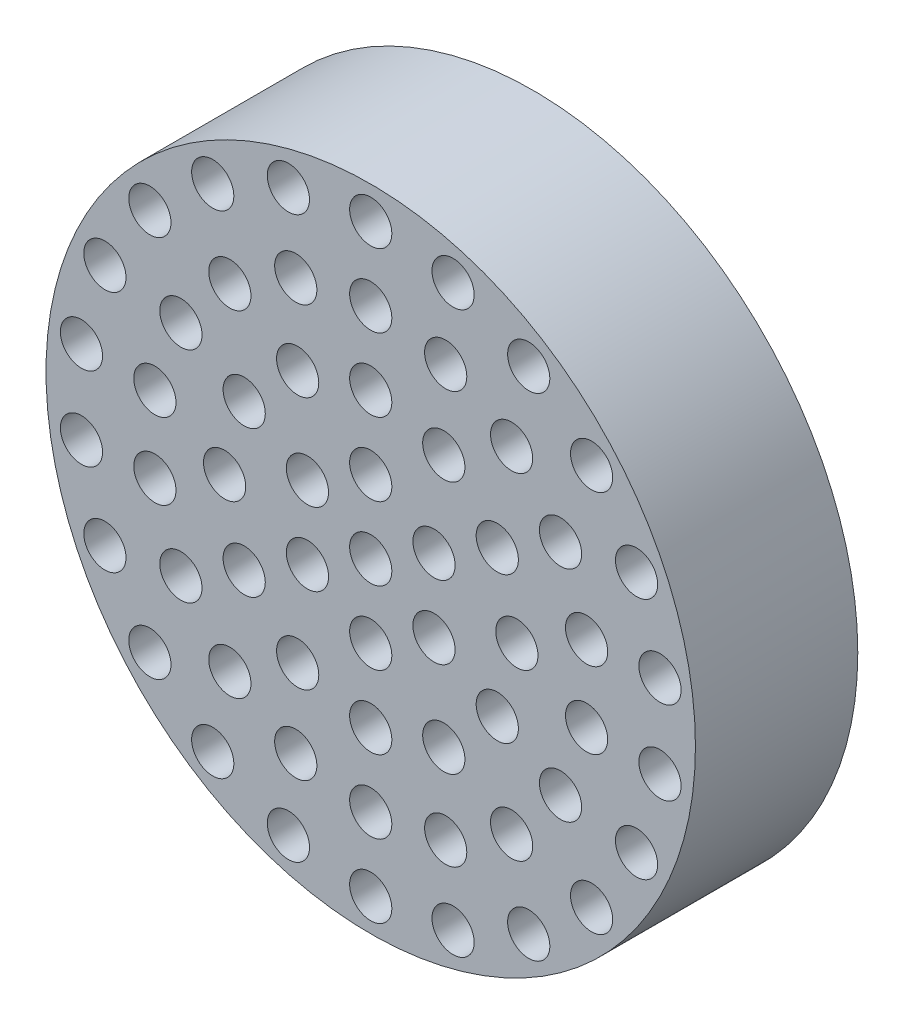
SolidWorks part; units mm, degrees
ref_plane "Plan de face" through (0, 0, 0) normal (0, 0, 1) x (1, 0, 0)
ref_plane "Plan de dessus" through (0, 0, 0) normal (0, 1, 0) x (1, 0, 0)
ref_plane "Plan de droite" through (0, 0, 0) normal (1, 0, 0) x (0, 0, -1)
sketch "Esquisse1" plane through (0, 0, 0) normal (0, 0, 1) x (1, 0, 0)
  line L0 (0, 0) -> (57.9765, 0) construction
  line L1 (0, 0) -> (0, 27.5754) construction
  circle A101 centre (0, 0) radius 20
  dimension "D1" = 40
extrude "Boss.-Extru.1" add sketch "Esquisse1" along normal blind 10
sketch "Esquisse2" plane through (0, 0, 10) normal (0, 0, 1) x (1, 0, 0)
  circle A1 centre (0, 4.5) radius 1.3
  circle A2 centre (-3.8971, 2.25) radius 1.3
  circle A3 centre (-3.8971, -2.25) radius 1.3
  circle A4 centre (0, -4.5) radius 1.3
  circle A5 centre (3.8971, -2.25) radius 1.3
  circle A6 centre (3.8971, 2.25) radius 1.3
  circle A7 centre (0, 0) radius 1.3
  circle A8 centre (0, 9) radius 1.3
  circle A9 centre (4.5, 7.7942) radius 1.3
  circle A10 centre (7.7942, 4.5) radius 1.3
  circle A11 centre (9, 0) radius 1.3
  circle A12 centre (7.7942, -4.5) radius 1.3
  circle A13 centre (4.5, -7.7942) radius 1.3
  circle A14 centre (0, -9) radius 1.3
  circle A15 centre (-4.5, -7.7942) radius 1.3
  circle A16 centre (-7.7942, -4.5) radius 1.3
  circle A17 centre (-9, 0) radius 1.3
  circle A18 centre (-7.7942, 4.5) radius 1.3
  circle A19 centre (-4.5, 7.7942) radius 1.3
  circle A20 centre (0, 13.5) radius 1.3
  circle A21 centre (0, 18) radius 1.3
  circle A22 centre (4.6173, 12.6859) radius 1.3
  circle A23 centre (8.6776, 10.3416) radius 1.3
  circle A24 centre (11.6913, 6.75) radius 1.3
  circle A25 centre (13.2949, 2.3443) radius 1.3
  circle A26 centre (13.2949, -2.3443) radius 1.3
  circle A27 centre (11.6913, -6.75) radius 1.3
  circle A28 centre (8.6776, -10.3416) radius 1.3
  circle A29 centre (4.6173, -12.6859) radius 1.3
  circle A30 centre (0, -13.5) radius 1.3
  circle A31 centre (-4.6173, -12.6859) radius 1.3
  circle A32 centre (-8.6776, -10.3416) radius 1.3
  circle A33 centre (-11.6913, -6.75) radius 1.3
  circle A34 centre (-13.2949, -2.3443) radius 1.3
  circle A35 centre (-13.2949, 2.3443) radius 1.3
  circle A36 centre (-11.6913, 6.75) radius 1.3
  circle A37 centre (-8.6776, 10.3416) radius 1.3
  circle A38 centre (-4.6173, 12.6859) radius 1.3
  circle A39 centre (5.0712, 17.2709) radius 1.3
  circle A40 centre (9.7315, 15.1426) radius 1.3
  circle A41 centre (13.6035, 11.7875) radius 1.3
  circle A42 centre (16.3734, 7.4775) radius 1.3
  circle A43 centre (17.8168, 2.5617) radius 1.3
  circle A44 centre (17.8168, -2.5617) radius 1.3
  circle A45 centre (16.3734, -7.4775) radius 1.3
  circle A46 centre (13.6035, -11.7875) radius 1.3
  circle A47 centre (9.7315, -15.1426) radius 1.3
  circle A48 centre (5.0712, -17.2709) radius 1.3
  circle A49 centre (0, -18) radius 1.3
  circle A50 centre (-5.0712, -17.2709) radius 1.3
  circle A51 centre (-9.7315, -15.1426) radius 1.3
  circle A52 centre (-13.6035, -11.7875) radius 1.3
  circle A53 centre (-16.3734, -7.4775) radius 1.3
  circle A54 centre (-17.8168, -2.5617) radius 1.3
  circle A55 centre (-17.8168, 2.5617) radius 1.3
  circle A56 centre (-16.3734, 7.4775) radius 1.3
  circle A57 centre (-13.6035, 11.7875) radius 1.3
  circle A58 centre (-9.7315, 15.1426) radius 1.3
  circle A59 centre (-5.0712, 17.2709) radius 1.3
  point P17 (0, 0)
  point P42 (0, 0)
  point P82 (0, 0)
  point P124 (0, 0)
  dimension "D1" = 2.6
  dimension "D4" = 2.6
  dimension "D5" = 2.6
  dimension "D8" = 2.6
  dimension "D9" = 2.6
  dimension "D2" = 4.5
  dimension "D6" = 4.5
  dimension "D10" = 4.5
  dimension "D11" = 4.5
  dimension "D3" = 6
  dimension "D7" = 12
  dimension "D12" = 18
  dimension "D13" = 22
extrude "Enlèv. mat.-Extru.1" cut sketch "Esquisse2" against normal up to next (10 mm away)
